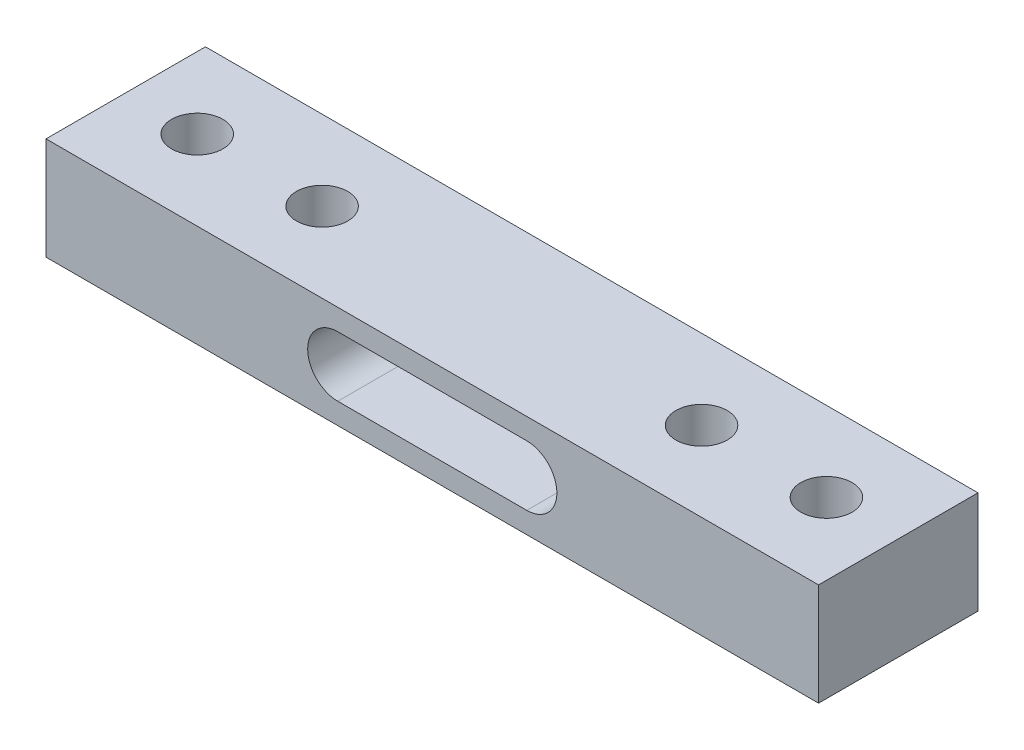
SolidWorks part; units mm, degrees
ref_plane "Front Plane" through (0, 0, 0) normal (0, 0, 1) x (1, 0, 0)
ref_plane "Top Plane" through (0, 0, 0) normal (0, 1, 0) x (1, 0, 0)
ref_plane "Right Plane" through (0, 0, 0) normal (1, 0, 0) x (0, 0, -1)
sketch "Sketch1" plane through (0, 0, 0) normal (0, 0, 1) x (1, 0, 0)
  line L0 (5.5236, 0) -> (-5.5236, 0) construction
  line L1 (-22.58, 2.995) -> (22.58, 2.995)
  line L2 (-22.58, 2.995) -> (-22.58, -2.995)
  line L3 (-22.58, -2.995) -> (22.58, -2.995)
  line L4 (22.58, 2.995) -> (22.58, -2.995)
  line L5 (-22.58, 2.995) -> (22.58, -2.995) construction
  line L6 (-22.58, -2.995) -> (22.58, 2.995) construction
  line L7 (5.5236, -1.7604) -> (-5.5236, -1.7604)
  line L8 (5.5236, 1.7604) -> (-5.5236, 1.7604)
  arc A0 (5.5236, -1.7604) -> (5.5236, 1.7604) centre (5.5236, 0) ccw
  arc A1 (-5.5236, 1.7604) -> (-5.5236, -1.7604) centre (-5.5236, 0) ccw
  point P0 (0, 0)
  point P8 (0, 0)
  dimension "D1" = 45.16
  dimension "D2" = 5.99
extrude "Boss-Extrude1" add sketch "Sketch1" along normal blind 9.32
sketch "Sketch2" plane through (0, 2.995, 0) normal (0, 1, 0) x (1, 0, 0)
  line L0 (-22.58, -4.66) -> (25.5596, -4.66) construction
  line L1 (-22.58, -9.32) -> (-22.58, 0) construction
  point P4 (-18.4, -4.66)
  point P5 (-11.1, -4.66)
  point P6 (11.08, -4.66)
  point P7 (18.38, -4.66)
  dimension "D1" = 4.18
  dimension "D2" = 7.3
  dimension "D3" = 22.18
  dimension "D4" = 7.3
hole_wizard "Ø3.0mm Dowel Hole1" positions "Sketch4" profile "Sketch3" hole size "Ø3.0" standard "ANSI Metric"
sketch "Sketch4" plane through (0, 2.995, 0) normal (0, 1, 0) x (1, 0, 0)
  point P0 (-18.4, -4.66)
  point P14 (-11.1, -4.66)
  point P17 (11.08, -4.66)
  point P20 (18.38, -4.66)
sketch "Sketch3" plane through (-18.4, 2.995, 4.66) normal (1, 0, 0) x (0, 0, 1)
  line L0 (0, 0) -> (0, 10.9013)
  line L1 (0, 10.9013) -> (1.5, 10)
  line L2 (1.5, 10) -> (1.5, 0)
  line L5 (1.5, 0) -> (0, 0)
  line L10 (0, 10.9013) -> (-1.5, 10) construction
  line L11 (0, -6.35) -> (0, 107.95) construction
  dimension "Hole Dia." = 3
  dimension "Hole Depth" = 10
  dimension "Drill Angle" = 118
